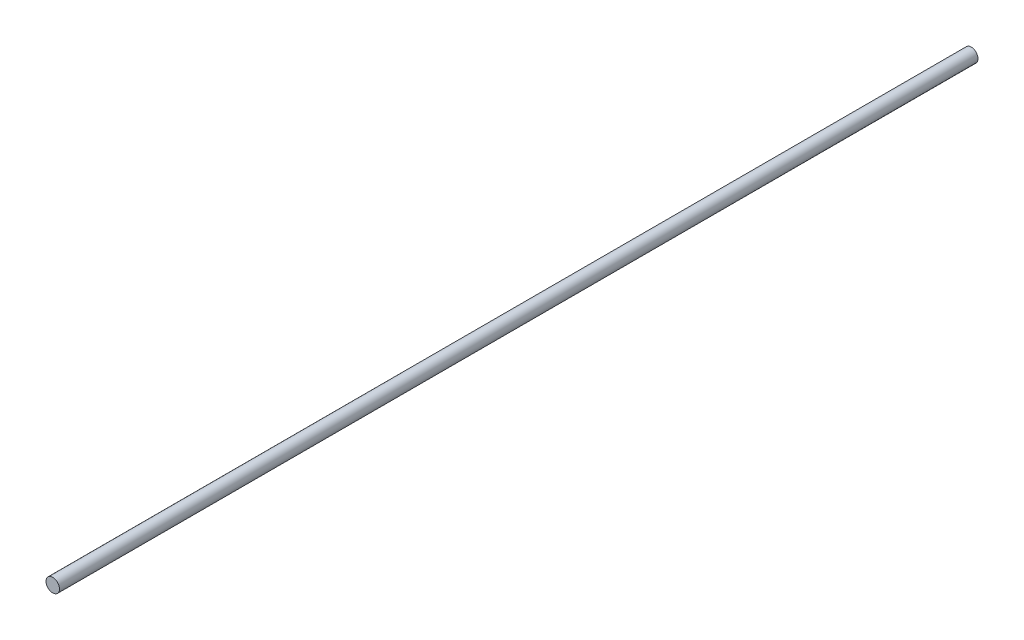
SolidWorks part; units mm, degrees
ref_plane "Front Plane" through (0, 0, 0) normal (0, 0, 1) x (1, 0, 0)
ref_plane "Top Plane" through (0, 0, 0) normal (0, 1, 0) x (1, 0, 0)
ref_plane "Right Plane" through (0, 0, 0) normal (1, 0, 0) x (0, 0, -1)
sketch "Sketch1" plane through (0, 0, 0) normal (0, 0, 1) x (1, 0, 0)
  circle A0 centre (0, 0) radius 0.3175
  dimension "D1" = 0.635
extrude "Boss-Extrude1" add sketch "Sketch1" along normal blind 43.18
